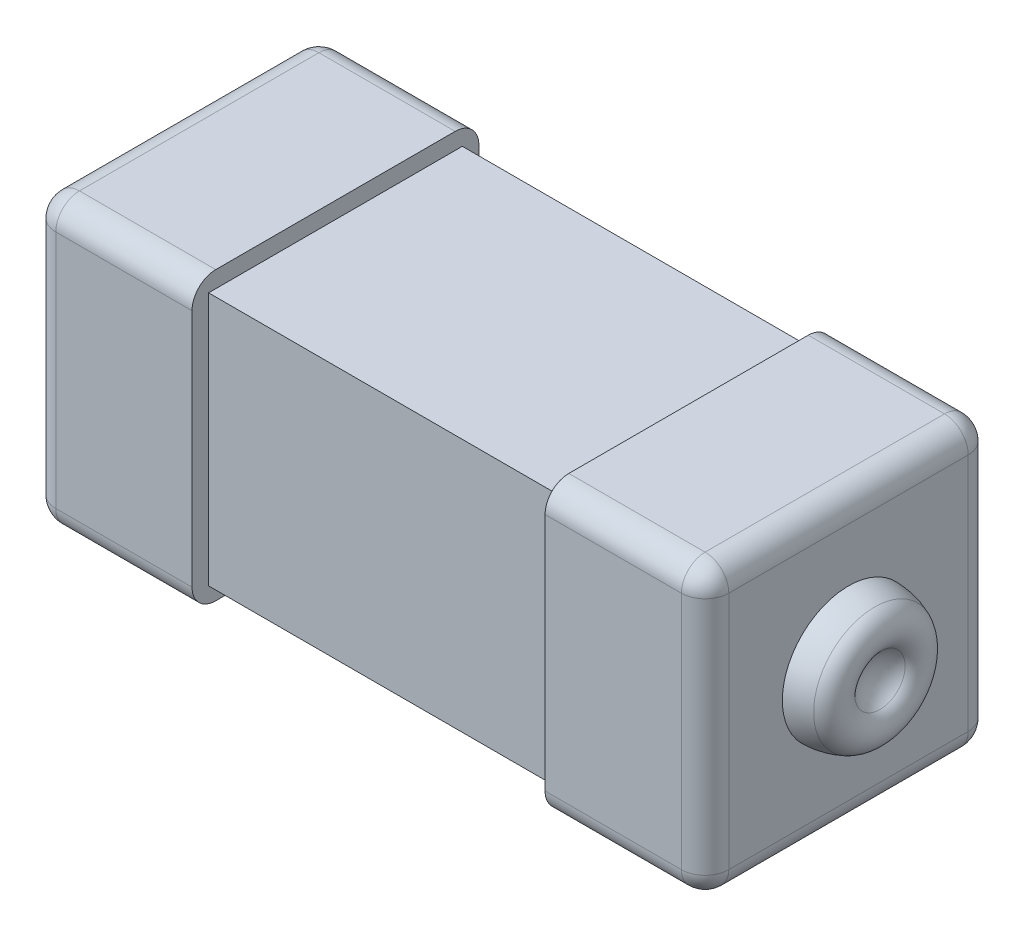
SolidWorks part; units mm, degrees
ref_plane "Front Plane" through (0, 0, 0) normal (0, 0, 1) x (1, 0, 0)
ref_plane "Top Plane" through (0, 0, 0) normal (0, 1, 0) x (1, 0, 0)
ref_plane "Right Plane" through (0, 0, 0) normal (1, 0, 0) x (0, 0, -1)
sketch "Sketch1" plane through (0, 0, 0) normal (1, 0, 0) x (0, 0, -1)
  line L0 (1.15, -1.15) -> (-1.15, 1.15) construction
  line L1 (-1.15, 1.15) -> (1.15, 1.15)
  line L2 (-1.15, 1.15) -> (-1.15, -1.15)
  line L3 (-1.15, -1.15) -> (1.15, -1.15)
  line L4 (1.15, 1.15) -> (1.15, -1.15)
  dimension "D1" = 2.3
extrude "Boss-Extrude1" add sketch "Sketch1" along normal mid plane 3.2
sketch "Sketch4" plane through (1.6, 0, 0) normal (1, 0, 0) x (0, 0, -1)
  line L0 (1.3, -1.3) -> (-1.3, 1.3) construction
  line L1 (-1.3, -1.3) -> (1.3, -1.3)
  line L2 (-1.3, -1.3) -> (-1.3, 1.3)
  line L3 (-1.3, 1.3) -> (1.3, 1.3)
  line L4 (1.3, -1.3) -> (1.3, 1.3)
  dimension "D1" = 2.6
extrude "Boss-Extrude2" add sketch "Sketch4" along normal blind 1.45
sketch "Sketch5" plane through (0, 0, 0) normal (0, 1, 0) x (1, 0, 0)
  line L0 (3.05, 1.3) -> (3.05, -1.3) construction
  line L1 (3.53, 0) -> (3.05, 0) construction
  line L2 (3.05, 0.6) -> (3.05, 0)
  line L3 (3.23, 0) -> (3.05, 0)
  arc A0 (3.2857, 0.5518) -> (3.05, 0.6) centre (3.05, 0) ccw
  arc A1 (3.3351, 0.2281) -> (3.23, 0) centre (3.53, 0) ccw
  arc A3 (3.3351, 0.2281) -> (3.2857, 0.5518) centre (3.21, 0.3746) ccw
  point P6 (3.23, 0)
  dimension "D1" = 1.2
  dimension "D3" = 0.6
  dimension "D4" = 0.16
  dimension "D2" = 0.18
revolve "Revolve4" add sketch "Sketch5" angle 360 about L1
fillet "Fillet1" radius 0.215 8 edges at (2.325, 1.3, 1.3) (3.05, 0, 1.3) (2.325, -1.3, 1.3) (2.325, -1.3, -1.3) (2.325, 1.3, -1.3) (3.05, 0, -1.3) (3.05, -1.3, 0) (3.05, 1.3, 0)
mirror "Mirror2" about plane through (0, 0, 0) normal (1, 0, 0) of "Boss-Extrude2", "Revolve4", "Fillet1"
